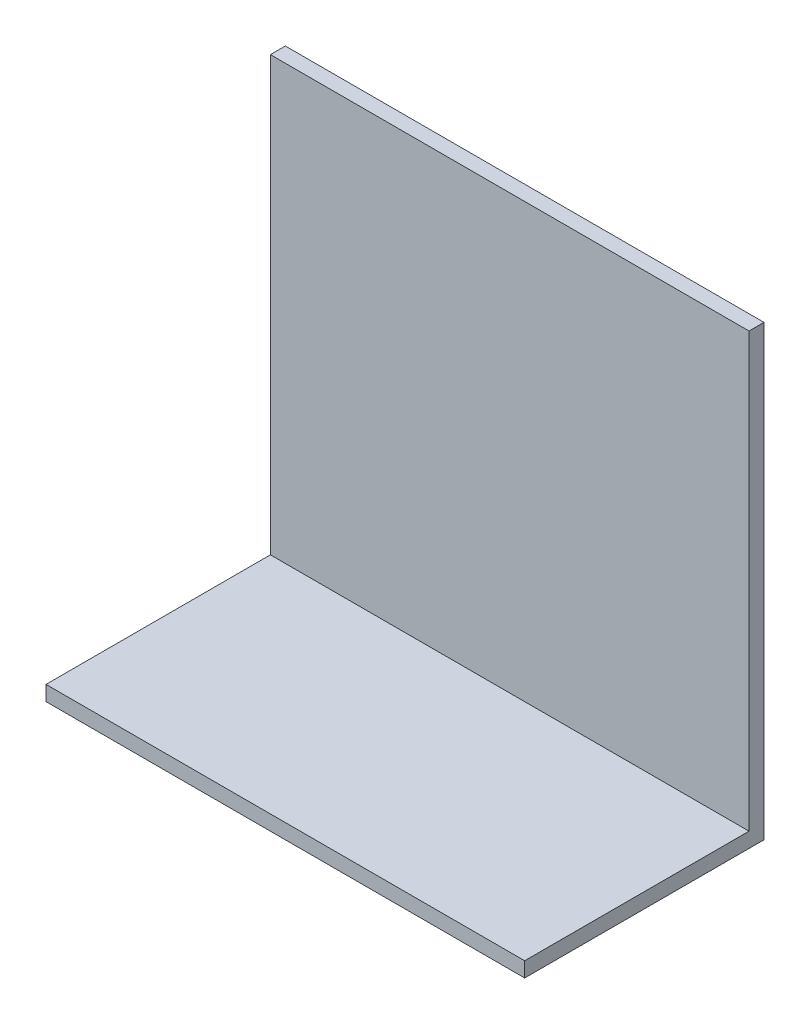
SolidWorks part; units mm, degrees
ref_plane "Front Plane" through (0, 0, 0) normal (0, 0, 1) x (1, 0, 0)
ref_plane "Top Plane" through (0, 0, 0) normal (0, 1, 0) x (1, 0, 0)
ref_plane "Right Plane" through (0, 0, 0) normal (1, 0, 0) x (0, 0, -1)
sketch "Sketch1" plane through (0, 0, 0) normal (0, 0, 1) x (1, 0, 0)
  line L1 (-46.2158, 66.383) -> (55.3842, 66.383)
  line L2 (-46.2158, 66.383) -> (-46.2158, -28.74)
  line L3 (-46.2158, -28.74) -> (55.3842, -28.74)
  line L4 (55.3842, 66.383) -> (55.3842, -28.74)
  point P4 (0, 0)
  dimension "D1" = 101.6
  dimension "D2" = 95.123
extrude "Boss-Extrude1" add sketch "Sketch1" along normal blind 3.175
sketch "Sketch2" plane through (0, -28.74, 0) normal (0, -1, 0) x (-1, 0, 0)
  line L0 (-55.3842, -3.175) -> (-55.3842, 0) construction
  line L1 (46.2158, 0) -> (-55.3842, 0)
  line L2 (46.2158, 0) -> (46.2158, -50.8)
  line L3 (46.2158, -50.8) -> (-55.3842, -50.8)
  line L4 (-55.3842, 0) -> (-55.3842, -50.8)
  line L5 (46.2158, 0) -> (-55.3842, 0) construction
  dimension "D1" = 101.6
  dimension "D2" = 50.8
  dimension "D3" = 0
  dimension "D4" = 0
extrude "Boss-Extrude2" add sketch "Sketch2" against normal blind 3.175 contours L2 L1 L4 L3
